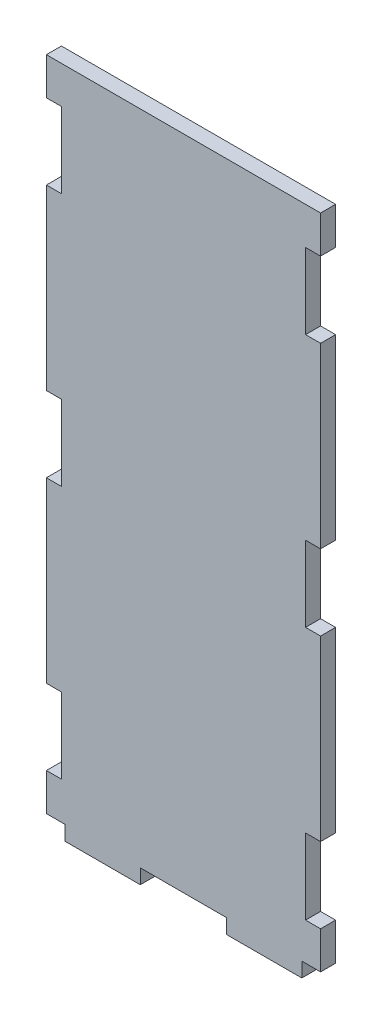
SolidWorks part; units mm, degrees
material "MDF"
ref_plane "正面" through (0, 0, 0) normal (1, 0, 0) x (0, 1, 0)
ref_plane "平面" through (0, 0, 0) normal (0, 0, 1) x (0, 1, 0)
ref_plane "右側面" through (0, 0, 0) normal (0, 1, 0) x (-1, 0, 0)
sketch "ｽｹｯﾁ1" plane through (0, 0, 0) normal (0, 0, 1) x (0, 1, 0)
  line L0 (-3.9, 5) -> (-3.9, 25)
  line L1 (0, 0) -> (175, 0)
  line L2 (0, 0) -> (0, 73)
  line L3 (0, 73) -> (175, 73)
  line L4 (175, 0) -> (175, 73)
  line L5 (87.5, 73) -> (87.5, 0) construction
  line L6 (0, 36.5) -> (175, 36.5) construction
  line L7 (0, 68) -> (-3.9, 68)
  line L8 (0, 68) -> (0, 48)
  line L9 (0, 48) -> (-3.9, 48)
  line L10 (-3.9, 68) -> (-3.9, 48)
  line L11 (0, 25) -> (-3.9, 25)
  line L12 (0, 5) -> (0, 25)
  line L13 (0, 5) -> (-3.9, 5)
  line L22 (9.95, 0) -> (30.05, 0)
  line L23 (9.95, 69) -> (30.05, 69)
  line L24 (9.95, 69) -> (9.95, 73)
  line L25 (9.95, 73) -> (30.05, 73)
  line L26 (30.05, 69) -> (30.05, 73)
  line L27 (30.05, 4) -> (30.05, 0)
  line L28 (9.95, 4) -> (30.05, 4)
  line L29 (9.95, 4) -> (9.95, 0)
  line L30 (165.05, 4) -> (165.05, 0)
  line L31 (165.05, 4) -> (144.95, 4)
  line L32 (144.95, 4) -> (144.95, 0)
  line L33 (165.05, 0) -> (144.95, 0)
  line L34 (165.05, 73) -> (144.95, 73)
  line L35 (144.95, 69) -> (144.95, 73)
  line L36 (165.05, 69) -> (144.95, 69)
  line L37 (165.05, 69) -> (165.05, 73)
  line L38 (77.45, 0) -> (97.55, 0)
  line L39 (77.45, 69) -> (97.55, 69)
  line L40 (77.45, 69) -> (77.45, 73)
  line L41 (77.45, 73) -> (97.55, 73)
  line L42 (97.55, 69) -> (97.55, 73)
  line L43 (97.55, 4) -> (97.55, 0)
  line L44 (77.45, 4) -> (97.55, 4)
  line L45 (77.45, 4) -> (77.45, 0)
  point P8 (0, 0)
  point P13 (0, 0)
  point P14 (0, 0)
  point P41 (87.5, 69)
  point P46 (20, 73)
  point P116 (87.5, 36.5)
  dimension "D1" = 175
  dimension "D2" = 73
  dimension "D3" = 20
  dimension "D4" = 3.9
  dimension "D5" = 11.5
  dimension "D6" = 20.1
  dimension "D7" = 4
  dimension "D8" = 20
  dimension "D9" = 20.1
  dimension "D10" = 4
extrude "ﾎﾞｽ - 押し出し1" add sketch "ｽｹｯﾁ1" along normal blind 4
